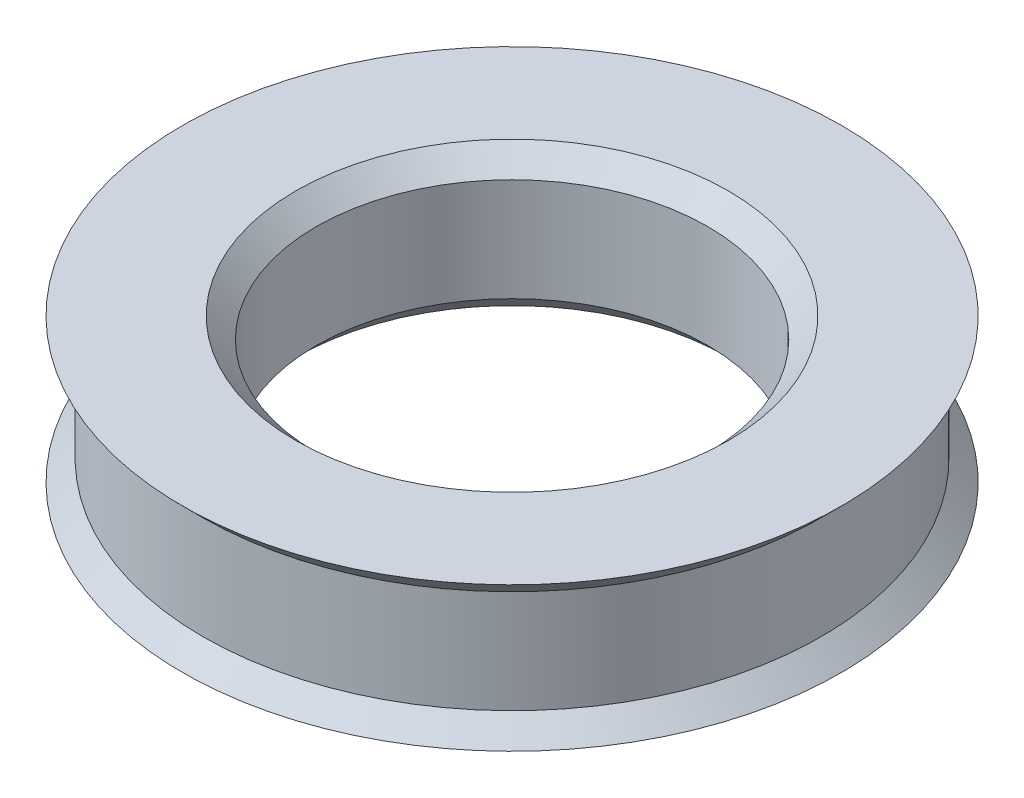
SolidWorks part; units mm, degrees
ref_plane "Front Plane" through (0, 0, 0) normal (0, 0, 1) x (1, 0, 0)
ref_plane "Top Plane" through (0, 0, 0) normal (0, 1, 0) x (1, 0, 0)
ref_plane "Right Plane" through (0, 0, 0) normal (1, 0, 0) x (0, 0, -1)
sketch "Sketch2" plane through (0, 0, 0) normal (0, 0, 1) x (1, 0, 0)
  line L0 (9.5, 3.5) -> (9.5, -3.5)
  line L1 (9.5, -3.5) -> (16, -3.5)
  line L2 (16, -3.5) -> (15, -2.5)
  line L3 (15, -2.5) -> (15, 2.5)
  line L4 (15, 2.5) -> (16, 3.5)
  line L5 (16, 3.5) -> (9.5, 3.5)
  line L6 (0, 0) -> (0, 1.5165) construction
  point P2 (15, 0)
  point P7 (9.5, 0)
  dimension "D1" = 7
  dimension "D2" = 5
  dimension "D3" = 15
  dimension "D4" = 9.5
revolve "Revolve1" add sketch "Sketch2" angle 360 about L6
chamfer "Chamfer1" distance 1 angle 45 2 edges at (0, 3.5, -9.5) (0, -3.5, -9.5)
